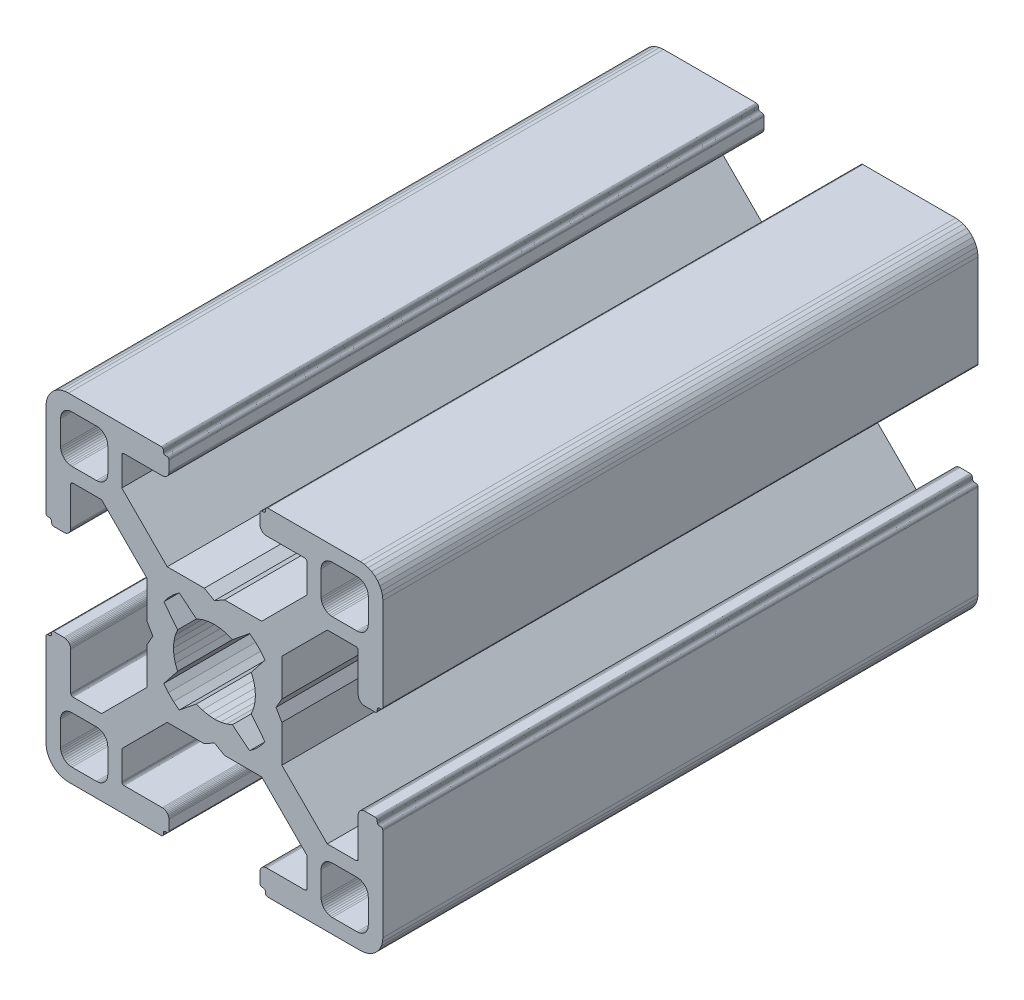
SolidWorks part; units mm, degrees
ref_plane "Front Plane" through (0, 0, 0) normal (0, 0, 1) x (1, 0, 0)
ref_plane "Top Plane" through (0, 0, 0) normal (0, 1, 0) x (1, 0, 0)
ref_plane "Right Plane" through (0, 0, 0) normal (1, 0, 0) x (0, 0, -1)
ref_plane "Plane1" through (0, 0, 0) normal (0, 0, 1) x (1, 0, 0)
sketch "Sketch1" plane through (0, 0, 0) normal (0, 0, 1) x (1, 0, 0)
  line L0 (28.3473, 29.9696) -> (28, 30)
  line L1 (28, 30) -> (19.75, 30)
  line L2 (19.75, 30) -> (19.7153, 29.997)
  line L3 (19.7153, 29.997) -> (19.6816, 29.9879)
  line L4 (19.6816, 29.9879) -> (19.65, 29.9732)
  line L5 (19.65, 29.9732) -> (19.6214, 29.9532)
  line L6 (19.6214, 29.9532) -> (19.5968, 29.9286)
  line L7 (19.5968, 29.9286) -> (19.5768, 29.9)
  line L8 (19.5768, 29.9) -> (19.5621, 29.8684)
  line L9 (19.5621, 29.8684) -> (19.553, 29.8347)
  line L10 (19.553, 29.8347) -> (19.55, 29.8)
  line L11 (19.55, 29.8) -> (19.55, 29.7)
  line L12 (19.55, 29.7) -> (19.547, 29.6653)
  line L13 (19.547, 29.6653) -> (19.5379, 29.6316)
  line L14 (19.5379, 29.6316) -> (19.5232, 29.6)
  line L15 (19.5232, 29.6) -> (19.5032, 29.5714)
  line L16 (19.5032, 29.5714) -> (19.4786, 29.5468)
  line L17 (19.4786, 29.5468) -> (19.45, 29.5268)
  line L18 (19.45, 29.5268) -> (19.4184, 29.5121)
  line L19 (19.4184, 29.5121) -> (19.3847, 29.503)
  line L20 (19.3847, 29.503) -> (19.35, 29.5)
  line L21 (19.35, 29.5) -> (19.25, 29.5)
  line L22 (19.25, 29.5) -> (19.2153, 29.497)
  line L23 (19.2153, 29.497) -> (19.1816, 29.4879)
  line L24 (19.1816, 29.4879) -> (19.15, 29.4732)
  line L25 (19.15, 29.4732) -> (19.1214, 29.4532)
  line L26 (19.1214, 29.4532) -> (19.0968, 29.4286)
  line L27 (19.0968, 29.4286) -> (19.0768, 29.4)
  line L28 (19.0768, 29.4) -> (19.0621, 29.3684)
  line L29 (19.0621, 29.3684) -> (19.053, 29.3347)
  line L30 (19.053, 29.3347) -> (19.05, 29.3)
  line L31 (19.05, 29.3) -> (19.05, 28.4)
  line L32 (19.05, 28.4) -> (19.0591, 28.2958)
  line L33 (19.0591, 28.2958) -> (19.0862, 28.1948)
  line L34 (19.0862, 28.1948) -> (19.1304, 28.1)
  line L35 (19.1304, 28.1) -> (19.1904, 28.0143)
  line L36 (19.1904, 28.0143) -> (19.2643, 27.9404)
  line L37 (19.2643, 27.9404) -> (19.35, 27.8804)
  line L38 (19.35, 27.8804) -> (19.4448, 27.8362)
  line L39 (19.4448, 27.8362) -> (19.5458, 27.8091)
  line L40 (19.5458, 27.8091) -> (19.65, 27.8)
  line L41 (19.65, 27.8) -> (23.05, 27.8)
  line L42 (23.05, 27.8) -> (23.0847, 27.7969)
  line L43 (23.0847, 27.7969) -> (23.1184, 27.7879)
  line L44 (23.1184, 27.7879) -> (23.15, 27.7732)
  line L45 (23.15, 27.7732) -> (23.1786, 27.7532)
  line L46 (23.1786, 27.7532) -> (23.2032, 27.7285)
  line L47 (23.2032, 27.7285) -> (23.2232, 27.7)
  line L48 (23.2232, 27.7) -> (23.2379, 27.6684)
  line L49 (23.2379, 27.6684) -> (23.247, 27.6347)
  line L50 (23.247, 27.6347) -> (23.25, 27.6)
  line L51 (23.25, 27.6) -> (23.25, 25.05)
  line L52 (23.25, 25.05) -> (19.2045, 21)
  line L53 (19.2045, 21) -> (15.9, 21)
  line L54 (15.9, 21) -> (15, 20.4848)
  line L55 (15, 20.4848) -> (14.1, 21)
  line L56 (14.1, 21) -> (10.7955, 21)
  line L57 (10.7955, 21) -> (7.9973, 23.8013)
  line L58 (7.9973, 23.8013) -> (6.75, 25.05)
  line L59 (6.75, 25.05) -> (6.75, 27.6)
  line L60 (6.75, 27.6) -> (6.753, 27.6347)
  line L61 (6.753, 27.6347) -> (6.7621, 27.6684)
  line L62 (6.7621, 27.6684) -> (6.7768, 27.7)
  line L63 (6.7768, 27.7) -> (6.7968, 27.7285)
  line L64 (6.7968, 27.7285) -> (6.8215, 27.7532)
  line L65 (6.8215, 27.7532) -> (6.85, 27.7732)
  line L66 (6.85, 27.7732) -> (6.8816, 27.7879)
  line L67 (6.8816, 27.7879) -> (6.9153, 27.7969)
  line L68 (6.9153, 27.7969) -> (6.95, 27.8)
  line L69 (6.95, 27.8) -> (10.35, 27.8)
  line L70 (10.35, 27.8) -> (10.4542, 27.8091)
  line L71 (10.4542, 27.8091) -> (10.5552, 27.8362)
  line L72 (10.5552, 27.8362) -> (10.65, 27.8804)
  line L73 (10.65, 27.8804) -> (10.7357, 27.9404)
  line L74 (10.7357, 27.9404) -> (10.8096, 28.0143)
  line L75 (10.8096, 28.0143) -> (10.8696, 28.1)
  line L76 (10.8696, 28.1) -> (10.9138, 28.1948)
  line L77 (10.9138, 28.1948) -> (10.9409, 28.2958)
  line L78 (10.9409, 28.2958) -> (10.95, 28.4)
  line L79 (10.95, 28.4) -> (10.95, 29.3)
  line L80 (10.95, 29.3) -> (10.947, 29.3347)
  line L81 (10.947, 29.3347) -> (10.938, 29.3684)
  line L82 (10.938, 29.3684) -> (10.9232, 29.4)
  line L83 (10.9232, 29.4) -> (10.9032, 29.4286)
  line L84 (10.9032, 29.4286) -> (10.8786, 29.4532)
  line L85 (10.8786, 29.4532) -> (10.85, 29.4732)
  line L86 (10.85, 29.4732) -> (10.8184, 29.4879)
  line L87 (10.8184, 29.4879) -> (10.7847, 29.497)
  line L88 (10.7847, 29.497) -> (10.75, 29.5)
  line L89 (10.75, 29.5) -> (10.65, 29.5)
  line L90 (10.65, 29.5) -> (10.6153, 29.503)
  line L91 (10.6153, 29.503) -> (10.5816, 29.5121)
  line L92 (10.5816, 29.5121) -> (10.55, 29.5268)
  line L93 (10.55, 29.5268) -> (10.5214, 29.5468)
  line L94 (10.5214, 29.5468) -> (10.4968, 29.5714)
  line L95 (10.4968, 29.5714) -> (10.4768, 29.6)
  line L96 (10.4768, 29.6) -> (10.4621, 29.6316)
  line L97 (10.4621, 29.6316) -> (10.453, 29.6653)
  line L98 (10.453, 29.6653) -> (10.45, 29.7)
  line L99 (10.45, 29.7) -> (10.45, 29.8)
  line L100 (10.45, 29.8) -> (10.447, 29.8347)
  line L101 (10.447, 29.8347) -> (10.4379, 29.8684)
  line L102 (10.4379, 29.8684) -> (10.4232, 29.9)
  line L103 (10.4232, 29.9) -> (10.4032, 29.9286)
  line L104 (10.4032, 29.9286) -> (10.3786, 29.9532)
  line L105 (10.3786, 29.9532) -> (10.35, 29.9732)
  line L106 (10.35, 29.9732) -> (10.3184, 29.9879)
  line L107 (10.3184, 29.9879) -> (10.2847, 29.997)
  line L108 (10.2847, 29.997) -> (10.25, 30)
  line L109 (10.25, 30) -> (2, 30)
  line L110 (2, 30) -> (1.6527, 29.9696)
  line L111 (1.6527, 29.9696) -> (1.316, 29.8794)
  line L112 (1.316, 29.8794) -> (1, 29.7321)
  line L113 (1, 29.7321) -> (0.7144, 29.5321)
  line L114 (0.7144, 29.5321) -> (0.4679, 29.2856)
  line L115 (0.4679, 29.2856) -> (0.2679, 29)
  line L116 (0.2679, 29) -> (0.1206, 28.684)
  line L117 (0.1206, 28.684) -> (0.0304, 28.3473)
  line L118 (0.0304, 28.3473) -> (0, 28)
  line L119 (0, 28) -> (0, 19.75)
  line L120 (0, 19.75) -> (0.003, 19.7153)
  line L121 (0.003, 19.7153) -> (0.0121, 19.6816)
  line L122 (0.0121, 19.6816) -> (0.0268, 19.65)
  line L123 (0.0268, 19.65) -> (0.0468, 19.6214)
  line L124 (0.0468, 19.6214) -> (0.0714, 19.5968)
  line L125 (0.0714, 19.5968) -> (0.1, 19.5768)
  line L126 (0.1, 19.5768) -> (0.1316, 19.5621)
  line L127 (0.1316, 19.5621) -> (0.1653, 19.553)
  line L128 (0.1653, 19.553) -> (0.2, 19.55)
  line L129 (0.2, 19.55) -> (0.3, 19.55)
  line L130 (0.3, 19.55) -> (0.3347, 19.547)
  line L131 (0.3347, 19.547) -> (0.3684, 19.5379)
  line L132 (0.3684, 19.5379) -> (0.4, 19.5232)
  line L133 (0.4, 19.5232) -> (0.4286, 19.5032)
  line L134 (0.4286, 19.5032) -> (0.4532, 19.4786)
  line L135 (0.4532, 19.4786) -> (0.4732, 19.45)
  line L136 (0.4732, 19.45) -> (0.4879, 19.4184)
  line L137 (0.4879, 19.4184) -> (0.497, 19.3847)
  line L138 (0.497, 19.3847) -> (0.5, 19.35)
  line L139 (0.5, 19.35) -> (0.5, 19.25)
  line L140 (0.5, 19.25) -> (0.503, 19.2153)
  line L141 (0.503, 19.2153) -> (0.5121, 19.1816)
  line L142 (0.5121, 19.1816) -> (0.5268, 19.15)
  line L143 (0.5268, 19.15) -> (0.5468, 19.1214)
  line L144 (0.5468, 19.1214) -> (0.5714, 19.0968)
  line L145 (0.5714, 19.0968) -> (0.6, 19.0768)
  line L146 (0.6, 19.0768) -> (0.6316, 19.0621)
  line L147 (0.6316, 19.0621) -> (0.6653, 19.053)
  line L148 (0.6653, 19.053) -> (0.7, 19.05)
  line L149 (0.7, 19.05) -> (1.6, 19.05)
  line L150 (1.6, 19.05) -> (1.7042, 19.0591)
  line L151 (1.7042, 19.0591) -> (1.8052, 19.0862)
  line L152 (1.8052, 19.0862) -> (1.9, 19.1304)
  line L153 (1.9, 19.1304) -> (1.9857, 19.1904)
  line L154 (1.9857, 19.1904) -> (2.0596, 19.2643)
  line L155 (2.0596, 19.2643) -> (2.1196, 19.35)
  line L156 (2.1196, 19.35) -> (2.1638, 19.4448)
  line L157 (2.1638, 19.4448) -> (2.1909, 19.5458)
  line L158 (2.1909, 19.5458) -> (2.2, 19.65)
  line L159 (2.2, 19.65) -> (2.2, 23.05)
  line L160 (2.2, 23.05) -> (2.203, 23.0847)
  line L161 (2.203, 23.0847) -> (2.2121, 23.1184)
  line L162 (2.2121, 23.1184) -> (2.2268, 23.15)
  line L163 (2.2268, 23.15) -> (2.2468, 23.1786)
  line L164 (2.2468, 23.1786) -> (2.2714, 23.2032)
  line L165 (2.2714, 23.2032) -> (2.3, 23.2232)
  line L166 (2.3, 23.2232) -> (2.3316, 23.2379)
  line L167 (2.3316, 23.2379) -> (2.3653, 23.247)
  line L168 (2.3653, 23.247) -> (2.4, 23.25)
  line L169 (2.4, 23.25) -> (4.95, 23.25)
  line L170 (4.95, 23.25) -> (7.9973, 20.2027)
  line L171 (7.9973, 20.2027) -> (8.9955, 19.2045)
  line L172 (8.9955, 19.2045) -> (8.9955, 15.9)
  line L173 (8.9955, 15.9) -> (9.5151, 15)
  line L174 (9.5151, 15) -> (8.9955, 14.1)
  line L175 (8.9955, 14.1) -> (8.9955, 10.7955)
  line L176 (8.9955, 10.7955) -> (4.95, 6.75)
  line L177 (4.95, 6.75) -> (2.4, 6.75)
  line L178 (2.4, 6.75) -> (2.3653, 6.753)
  line L179 (2.3653, 6.753) -> (2.3316, 6.7621)
  line L180 (2.3316, 6.7621) -> (2.3, 6.7768)
  line L181 (2.3, 6.7768) -> (2.2714, 6.7968)
  line L182 (2.2714, 6.7968) -> (2.2468, 6.8214)
  line L183 (2.2468, 6.8214) -> (2.2268, 6.85)
  line L184 (2.2268, 6.85) -> (2.2121, 6.8816)
  line L185 (2.2121, 6.8816) -> (2.203, 6.9153)
  line L186 (2.203, 6.9153) -> (2.2, 6.95)
  line L187 (2.2, 6.95) -> (2.2, 10.35)
  line L188 (2.2, 10.35) -> (2.1909, 10.4542)
  line L189 (2.1909, 10.4542) -> (2.1638, 10.5552)
  line L190 (2.1638, 10.5552) -> (2.1196, 10.65)
  line L191 (2.1196, 10.65) -> (2.0596, 10.7357)
  line L192 (2.0596, 10.7357) -> (1.9857, 10.8096)
  line L193 (1.9857, 10.8096) -> (1.9, 10.8696)
  line L194 (1.9, 10.8696) -> (1.8052, 10.9138)
  line L195 (1.8052, 10.9138) -> (1.7042, 10.9409)
  line L196 (1.7042, 10.9409) -> (1.6, 10.95)
  line L197 (1.6, 10.95) -> (0.7, 10.95)
  line L198 (0.7, 10.95) -> (0.6653, 10.9469)
  line L199 (0.6653, 10.9469) -> (0.6316, 10.9379)
  line L200 (0.6316, 10.9379) -> (0.6, 10.9232)
  line L201 (0.6, 10.9232) -> (0.5715, 10.9032)
  line L202 (0.5715, 10.9032) -> (0.5468, 10.8785)
  line L203 (0.5468, 10.8785) -> (0.5268, 10.85)
  line L204 (0.5268, 10.85) -> (0.5121, 10.8184)
  line L205 (0.5121, 10.8184) -> (0.503, 10.7847)
  line L206 (0.503, 10.7847) -> (0.5, 10.75)
  line L207 (0.5, 10.75) -> (0.5, 10.65)
  line L208 (0.5, 10.65) -> (0.497, 10.6153)
  line L209 (0.497, 10.6153) -> (0.4879, 10.5816)
  line L210 (0.4879, 10.5816) -> (0.4732, 10.55)
  line L211 (0.4732, 10.55) -> (0.4532, 10.5214)
  line L212 (0.4532, 10.5214) -> (0.4286, 10.4968)
  line L213 (0.4286, 10.4968) -> (0.4, 10.4768)
  line L214 (0.4, 10.4768) -> (0.3684, 10.4621)
  line L215 (0.3684, 10.4621) -> (0.3347, 10.453)
  line L216 (0.3347, 10.453) -> (0.3, 10.45)
  line L217 (0.3, 10.45) -> (0.2, 10.45)
  line L218 (0.2, 10.45) -> (0.1653, 10.447)
  line L219 (0.1653, 10.447) -> (0.1316, 10.4379)
  line L220 (0.1316, 10.4379) -> (0.1, 10.4232)
  line L221 (0.1, 10.4232) -> (0.0714, 10.4032)
  line L222 (0.0714, 10.4032) -> (0.0468, 10.3786)
  line L223 (0.0468, 10.3786) -> (0.0268, 10.35)
  line L224 (0.0268, 10.35) -> (0.0121, 10.3184)
  line L225 (0.0121, 10.3184) -> (0.003, 10.2847)
  line L226 (0.003, 10.2847) -> (0, 10.25)
  line L227 (0, 10.25) -> (0, 2)
  line L228 (0, 2) -> (0.0304, 1.6527)
  line L229 (0.0304, 1.6527) -> (0.1206, 1.316)
  line L230 (0.1206, 1.316) -> (0.2679, 1)
  line L231 (0.2679, 1) -> (0.4679, 0.7144)
  line L232 (0.4679, 0.7144) -> (0.7144, 0.4679)
  line L233 (0.7144, 0.4679) -> (1, 0.2679)
  line L234 (1, 0.2679) -> (1.316, 0.1206)
  line L235 (1.316, 0.1206) -> (1.6527, 0.0304)
  line L236 (1.6527, 0.0304) -> (2, 0)
  line L237 (2, 0) -> (10.25, 0)
  line L238 (10.25, 0) -> (10.2847, 0.003)
  line L239 (10.2847, 0.003) -> (10.3184, 0.0121)
  line L240 (10.3184, 0.0121) -> (10.35, 0.0268)
  line L241 (10.35, 0.0268) -> (10.3786, 0.0468)
  line L242 (10.3786, 0.0468) -> (10.4032, 0.0714)
  line L243 (10.4032, 0.0714) -> (10.4232, 0.1)
  line L244 (10.4232, 0.1) -> (10.4379, 0.1316)
  line L245 (10.4379, 0.1316) -> (10.447, 0.1653)
  line L246 (10.447, 0.1653) -> (10.45, 0.2)
  line L247 (10.45, 0.2) -> (10.45, 0.3)
  line L248 (10.45, 0.3) -> (10.453, 0.3347)
  line L249 (10.453, 0.3347) -> (10.4621, 0.3684)
  line L250 (10.4621, 0.3684) -> (10.4768, 0.4)
  line L251 (10.4768, 0.4) -> (10.4968, 0.4286)
  line L252 (10.4968, 0.4286) -> (10.5214, 0.4532)
  line L253 (10.5214, 0.4532) -> (10.55, 0.4732)
  line L254 (10.55, 0.4732) -> (10.5816, 0.4879)
  line L255 (10.5816, 0.4879) -> (10.6153, 0.497)
  line L256 (10.6153, 0.497) -> (10.65, 0.5)
  line L257 (10.65, 0.5) -> (10.75, 0.5)
  line L258 (10.75, 0.5) -> (10.7847, 0.503)
  line L259 (10.7847, 0.503) -> (10.8184, 0.5121)
  line L260 (10.8184, 0.5121) -> (10.85, 0.5268)
  line L261 (10.85, 0.5268) -> (10.8785, 0.5468)
  line L262 (10.8785, 0.5468) -> (10.9032, 0.5715)
  line L263 (10.9032, 0.5715) -> (10.9232, 0.6)
  line L264 (10.9232, 0.6) -> (10.9379, 0.6316)
  line L265 (10.9379, 0.6316) -> (10.9469, 0.6653)
  line L266 (10.9469, 0.6653) -> (10.95, 0.7)
  line L267 (10.95, 0.7) -> (10.95, 1.6)
  line L268 (10.95, 1.6) -> (10.9409, 1.7042)
  line L269 (10.9409, 1.7042) -> (10.9138, 1.8052)
  line L270 (10.9138, 1.8052) -> (10.8696, 1.9)
  line L271 (10.8696, 1.9) -> (10.8096, 1.9857)
  line L272 (10.8096, 1.9857) -> (10.7357, 2.0596)
  line L273 (10.7357, 2.0596) -> (10.65, 2.1196)
  line L274 (10.65, 2.1196) -> (10.5552, 2.1638)
  line L275 (10.5552, 2.1638) -> (10.4542, 2.1909)
  line L276 (10.4542, 2.1909) -> (10.35, 2.2)
  line L277 (10.35, 2.2) -> (6.95, 2.2)
  line L278 (6.95, 2.2) -> (6.9153, 2.203)
  line L279 (6.9153, 2.203) -> (6.8816, 2.212)
  line L280 (6.8816, 2.212) -> (6.85, 2.2268)
  line L281 (6.85, 2.2268) -> (6.8215, 2.2468)
  line L282 (6.8215, 2.2468) -> (6.7968, 2.2714)
  line L283 (6.7968, 2.2714) -> (6.7768, 2.3)
  line L284 (6.7768, 2.3) -> (6.7621, 2.3316)
  line L285 (6.7621, 2.3316) -> (6.753, 2.3653)
  line L286 (6.753, 2.3653) -> (6.75, 2.4)
  line L287 (6.75, 2.4) -> (6.75, 4.95)
  line L288 (6.75, 4.95) -> (9.7875, 7.9908)
  line L289 (9.7875, 7.9908) -> (10.7955, 9)
  line L290 (10.7955, 9) -> (14.1, 9)
  line L291 (14.1, 9) -> (15, 9.5151)
  line L292 (15, 9.5151) -> (15.9, 9)
  line L293 (15.9, 9) -> (19.2045, 9)
  line L294 (19.2045, 9) -> (20.2126, 7.9908)
  line L295 (20.2126, 7.9908) -> (23.25, 4.95)
  line L296 (23.25, 4.95) -> (23.25, 2.4)
  line L297 (23.25, 2.4) -> (23.247, 2.3653)
  line L298 (23.247, 2.3653) -> (23.2379, 2.3316)
  line L299 (23.2379, 2.3316) -> (23.2232, 2.3)
  line L300 (23.2232, 2.3) -> (23.2032, 2.2714)
  line L301 (23.2032, 2.2714) -> (23.1786, 2.2468)
  line L302 (23.1786, 2.2468) -> (23.15, 2.2268)
  line L303 (23.15, 2.2268) -> (23.1184, 2.212)
  line L304 (23.1184, 2.212) -> (23.0847, 2.203)
  line L305 (23.0847, 2.203) -> (23.05, 2.2)
  line L306 (23.05, 2.2) -> (19.65, 2.2)
  line L307 (19.65, 2.2) -> (19.5458, 2.1909)
  line L308 (19.5458, 2.1909) -> (19.4448, 2.1638)
  line L309 (19.4448, 2.1638) -> (19.35, 2.1196)
  line L310 (19.35, 2.1196) -> (19.2643, 2.0596)
  line L311 (19.2643, 2.0596) -> (19.1904, 1.9857)
  line L312 (19.1904, 1.9857) -> (19.1304, 1.9)
  line L313 (19.1304, 1.9) -> (19.0862, 1.8052)
  line L314 (19.0862, 1.8052) -> (19.0591, 1.7042)
  line L315 (19.0591, 1.7042) -> (19.05, 1.6)
  line L316 (19.05, 1.6) -> (19.05, 0.7)
  line L317 (19.05, 0.7) -> (19.053, 0.6653)
  line L318 (19.053, 0.6653) -> (19.0621, 0.6316)
  line L319 (19.0621, 0.6316) -> (19.0768, 0.6)
  line L320 (19.0768, 0.6) -> (19.0968, 0.5714)
  line L321 (19.0968, 0.5714) -> (19.1214, 0.5468)
  line L322 (19.1214, 0.5468) -> (19.15, 0.5268)
  line L323 (19.15, 0.5268) -> (19.1816, 0.5121)
  line L324 (19.1816, 0.5121) -> (19.2153, 0.503)
  line L325 (19.2153, 0.503) -> (19.25, 0.5)
  line L326 (19.25, 0.5) -> (19.35, 0.5)
  line L327 (19.35, 0.5) -> (19.3847, 0.497)
  line L328 (19.3847, 0.497) -> (19.4184, 0.4879)
  line L329 (19.4184, 0.4879) -> (19.45, 0.4732)
  line L330 (19.45, 0.4732) -> (19.4786, 0.4532)
  line L331 (19.4786, 0.4532) -> (19.5032, 0.4286)
  line L332 (19.5032, 0.4286) -> (19.5232, 0.4)
  line L333 (19.5232, 0.4) -> (19.5379, 0.3684)
  line L334 (19.5379, 0.3684) -> (19.547, 0.3347)
  line L335 (19.547, 0.3347) -> (19.55, 0.3)
  line L336 (19.55, 0.3) -> (19.55, 0.2)
  line L337 (19.55, 0.2) -> (19.553, 0.1653)
  line L338 (19.553, 0.1653) -> (19.5621, 0.1316)
  line L339 (19.5621, 0.1316) -> (19.5768, 0.1)
  line L340 (19.5768, 0.1) -> (19.5968, 0.0714)
  line L341 (19.5968, 0.0714) -> (19.6214, 0.0468)
  line L342 (19.6214, 0.0468) -> (19.65, 0.0268)
  line L343 (19.65, 0.0268) -> (19.6816, 0.0121)
  line L344 (19.6816, 0.0121) -> (19.7153, 0.003)
  line L345 (19.7153, 0.003) -> (19.75, 0)
  line L346 (19.75, 0) -> (28, 0)
  line L347 (28, 0) -> (28.3473, 0.0304)
  line L348 (28.3473, 0.0304) -> (28.684, 0.1206)
  line L349 (28.684, 0.1206) -> (29, 0.2679)
  line L350 (29, 0.2679) -> (29.2856, 0.4679)
  line L351 (29.2856, 0.4679) -> (29.5321, 0.7144)
  line L352 (29.5321, 0.7144) -> (29.7321, 1)
  line L353 (29.7321, 1) -> (29.8794, 1.316)
  line L354 (29.8794, 1.316) -> (29.9696, 1.6527)
  line L355 (29.9696, 1.6527) -> (30, 2)
  line L356 (30, 2) -> (30, 10.25)
  line L357 (30, 10.25) -> (29.997, 10.2847)
  line L358 (29.997, 10.2847) -> (29.988, 10.3184)
  line L359 (29.988, 10.3184) -> (29.9732, 10.35)
  line L360 (29.9732, 10.35) -> (29.9532, 10.3785)
  line L361 (29.9532, 10.3785) -> (29.9286, 10.4032)
  line L362 (29.9286, 10.4032) -> (29.9, 10.4232)
  line L363 (29.9, 10.4232) -> (29.8684, 10.4379)
  line L364 (29.8684, 10.4379) -> (29.8347, 10.447)
  line L365 (29.8347, 10.447) -> (29.8, 10.45)
  line L366 (29.8, 10.45) -> (29.7, 10.45)
  line L367 (29.7, 10.45) -> (29.6649, 10.4534)
  line L368 (29.6649, 10.4534) -> (29.6312, 10.4624)
  line L369 (29.6312, 10.4624) -> (29.5996, 10.4772)
  line L370 (29.5996, 10.4772) -> (29.5711, 10.4972)
  line L371 (29.5711, 10.4972) -> (29.5464, 10.5218)
  line L372 (29.5464, 10.5218) -> (29.5264, 10.5504)
  line L373 (29.5264, 10.5504) -> (29.5117, 10.582)
  line L374 (29.5117, 10.582) -> (29.5027, 10.6156)
  line L375 (29.5027, 10.6156) -> (29.4996, 10.6504)
  line L376 (29.4996, 10.6504) -> (29.4996, 10.7504)
  line L377 (29.4996, 10.7504) -> (29.497, 10.7847)
  line L378 (29.497, 10.7847) -> (29.4879, 10.8184)
  line L379 (29.4879, 10.8184) -> (29.4732, 10.85)
  line L380 (29.4732, 10.85) -> (29.4532, 10.8785)
  line L381 (29.4532, 10.8785) -> (29.4286, 10.9032)
  line L382 (29.4286, 10.9032) -> (29.4, 10.9232)
  line L383 (29.4, 10.9232) -> (29.3684, 10.9379)
  line L384 (29.3684, 10.9379) -> (29.3347, 10.9469)
  line L385 (29.3347, 10.9469) -> (29.3, 10.95)
  line L386 (29.3, 10.95) -> (28.4, 10.95)
  line L387 (28.4, 10.95) -> (28.2958, 10.9409)
  line L388 (28.2958, 10.9409) -> (28.1948, 10.9138)
  line L389 (28.1948, 10.9138) -> (28.1, 10.8696)
  line L390 (28.1, 10.8696) -> (28.0143, 10.8096)
  line L391 (28.0143, 10.8096) -> (27.9404, 10.7357)
  line L392 (27.9404, 10.7357) -> (27.8804, 10.65)
  line L393 (27.8804, 10.65) -> (27.8362, 10.5552)
  line L394 (27.8362, 10.5552) -> (27.8091, 10.4542)
  line L395 (27.8091, 10.4542) -> (27.8, 10.35)
  line L396 (27.8, 10.35) -> (27.8, 6.95)
  line L397 (27.8, 6.95) -> (27.797, 6.9153)
  line L398 (27.797, 6.9153) -> (27.7879, 6.8816)
  line L399 (27.7879, 6.8816) -> (27.7732, 6.85)
  line L400 (27.7732, 6.85) -> (27.7532, 6.8214)
  line L401 (27.7532, 6.8214) -> (27.7286, 6.7968)
  line L402 (27.7286, 6.7968) -> (27.7, 6.7768)
  line L403 (27.7, 6.7768) -> (27.6684, 6.7621)
  line L404 (27.6684, 6.7621) -> (27.6347, 6.753)
  line L405 (27.6347, 6.753) -> (27.6, 6.75)
  line L406 (27.6, 6.75) -> (25.05, 6.75)
  line L407 (25.05, 6.75) -> (23.8092, 7.9908)
  line L408 (23.8092, 7.9908) -> (21.0045, 10.7955)
  line L409 (21.0045, 10.7955) -> (21.0045, 14.1)
  line L410 (21.0045, 14.1) -> (20.4849, 15)
  line L411 (20.4849, 15) -> (21.0045, 15.9)
  line L412 (21.0045, 15.9) -> (21.0045, 19.2045)
  line L413 (21.0045, 19.2045) -> (25.05, 23.25)
  line L414 (25.05, 23.25) -> (27.6, 23.25)
  line L415 (27.6, 23.25) -> (27.6347, 23.247)
  line L416 (27.6347, 23.247) -> (27.6684, 23.2379)
  line L417 (27.6684, 23.2379) -> (27.7, 23.2232)
  line L418 (27.7, 23.2232) -> (27.7286, 23.2032)
  line L419 (27.7286, 23.2032) -> (27.7532, 23.1786)
  line L420 (27.7532, 23.1786) -> (27.7732, 23.15)
  line L421 (27.7732, 23.15) -> (27.7879, 23.1184)
  line L422 (27.7879, 23.1184) -> (27.797, 23.0847)
  line L423 (27.797, 23.0847) -> (27.8, 23.05)
  line L424 (27.8, 23.05) -> (27.8, 19.65)
  line L425 (27.8, 19.65) -> (27.8091, 19.5458)
  line L426 (27.8091, 19.5458) -> (27.8362, 19.4448)
  line L427 (27.8362, 19.4448) -> (27.8804, 19.35)
  line L428 (27.8804, 19.35) -> (27.9404, 19.2643)
  line L429 (27.9404, 19.2643) -> (28.0143, 19.1904)
  line L430 (28.0143, 19.1904) -> (28.1, 19.1304)
  line L431 (28.1, 19.1304) -> (28.1948, 19.0862)
  line L432 (28.1948, 19.0862) -> (28.2958, 19.0591)
  line L433 (28.2958, 19.0591) -> (28.4, 19.05)
  line L434 (28.4, 19.05) -> (29.3, 19.05)
  line L435 (29.3, 19.05) -> (29.3347, 19.053)
  line L436 (29.3347, 19.053) -> (29.3684, 19.0621)
  line L437 (29.3684, 19.0621) -> (29.4, 19.0768)
  line L438 (29.4, 19.0768) -> (29.4282, 19.0971)
  line L439 (29.4282, 19.0971) -> (29.4528, 19.1218)
  line L440 (29.4528, 19.1218) -> (29.4728, 19.1504)
  line L441 (29.4728, 19.1504) -> (29.4876, 19.182)
  line L442 (29.4876, 19.182) -> (29.4966, 19.2156)
  line L443 (29.4966, 19.2156) -> (29.4996, 19.2504)
  line L444 (29.4996, 19.2504) -> (29.4996, 19.3504)
  line L445 (29.4996, 19.3504) -> (29.5027, 19.3851)
  line L446 (29.5027, 19.3851) -> (29.5117, 19.4188)
  line L447 (29.5117, 19.4188) -> (29.5264, 19.4504)
  line L448 (29.5264, 19.4504) -> (29.5464, 19.4789)
  line L449 (29.5464, 19.4789) -> (29.5711, 19.5036)
  line L450 (29.5711, 19.5036) -> (29.5996, 19.5236)
  line L451 (29.5996, 19.5236) -> (29.6312, 19.5383)
  line L452 (29.6312, 19.5383) -> (29.6649, 19.5473)
  line L453 (29.6649, 19.5473) -> (29.7, 19.55)
  line L454 (29.7, 19.55) -> (29.8, 19.55)
  line L455 (29.8, 19.55) -> (29.8347, 19.553)
  line L456 (29.8347, 19.553) -> (29.8684, 19.5621)
  line L457 (29.8684, 19.5621) -> (29.9, 19.5768)
  line L458 (29.9, 19.5768) -> (29.9286, 19.5968)
  line L459 (29.9286, 19.5968) -> (29.9532, 19.6214)
  line L460 (29.9532, 19.6214) -> (29.9732, 19.65)
  line L461 (29.9732, 19.65) -> (29.9879, 19.6816)
  line L462 (29.9879, 19.6816) -> (29.997, 19.7153)
  line L463 (29.997, 19.7153) -> (30, 19.75)
  line L464 (30, 19.75) -> (30, 28)
  line L465 (30, 28) -> (29.9696, 28.3473)
  line L466 (29.9696, 28.3473) -> (29.8794, 28.684)
  line L467 (29.8794, 28.684) -> (29.7321, 29)
  line L468 (29.7321, 29) -> (29.5321, 29.2856)
  line L469 (29.5321, 29.2856) -> (29.2856, 29.5321)
  line L470 (29.2856, 29.5321) -> (29, 29.7321)
  line L471 (29, 29.7321) -> (28.684, 29.8794)
  line L472 (28.684, 29.8794) -> (28.3473, 29.9696)
  line L473 (1.3, 25.5) -> (1.3, 27.7)
  line L474 (1.3, 27.7) -> (1.3123, 27.8564)
  line L475 (1.3123, 27.8564) -> (1.3489, 28.009)
  line L476 (1.3489, 28.009) -> (1.409, 28.154)
  line L477 (1.409, 28.154) -> (1.491, 28.2878)
  line L478 (1.491, 28.2878) -> (1.5929, 28.4071)
  line L479 (1.5929, 28.4071) -> (1.7122, 28.509)
  line L480 (1.7122, 28.509) -> (1.846, 28.591)
  line L481 (1.846, 28.591) -> (1.991, 28.6511)
  line L482 (1.991, 28.6511) -> (2.1436, 28.6877)
  line L483 (2.1436, 28.6877) -> (2.3, 28.7)
  line L484 (2.3, 28.7) -> (4.5, 28.7)
  line L485 (4.5, 28.7) -> (4.6564, 28.6877)
  line L486 (4.6564, 28.6877) -> (4.809, 28.6511)
  line L487 (4.809, 28.6511) -> (4.954, 28.591)
  line L488 (4.954, 28.591) -> (5.0878, 28.509)
  line L489 (5.0878, 28.509) -> (5.2071, 28.4071)
  line L490 (5.2071, 28.4071) -> (5.309, 28.2878)
  line L491 (5.309, 28.2878) -> (5.391, 28.154)
  line L492 (5.391, 28.154) -> (5.4511, 28.009)
  line L493 (5.4511, 28.009) -> (5.4877, 27.8564)
  line L494 (5.4877, 27.8564) -> (5.5, 27.7)
  line L495 (5.5, 27.7) -> (5.5, 25.5)
  line L496 (5.5, 25.5) -> (5.4877, 25.3436)
  line L497 (5.4877, 25.3436) -> (5.4511, 25.191)
  line L498 (5.4511, 25.191) -> (5.391, 25.046)
  line L499 (5.391, 25.046) -> (5.309, 24.9122)
  line L500 (5.309, 24.9122) -> (5.2071, 24.7929)
  line L501 (5.2071, 24.7929) -> (5.0878, 24.691)
  line L502 (5.0878, 24.691) -> (4.954, 24.609)
  line L503 (4.954, 24.609) -> (4.809, 24.5489)
  line L504 (4.809, 24.5489) -> (4.6564, 24.5123)
  line L505 (4.6564, 24.5123) -> (4.5, 24.5)
  line L506 (4.5, 24.5) -> (2.3, 24.5)
  line L507 (2.3, 24.5) -> (2.1436, 24.5123)
  line L508 (2.1436, 24.5123) -> (1.991, 24.5489)
  line L509 (1.991, 24.5489) -> (1.846, 24.609)
  line L510 (1.846, 24.609) -> (1.7122, 24.691)
  line L511 (1.7122, 24.691) -> (1.5929, 24.7929)
  line L512 (1.5929, 24.7929) -> (1.491, 24.9122)
  line L513 (1.491, 24.9122) -> (1.409, 25.046)
  line L514 (1.409, 25.046) -> (1.3489, 25.191)
  line L515 (1.3489, 25.191) -> (1.3123, 25.3436)
  line L516 (1.3123, 25.3436) -> (1.3, 25.5)
  line L517 (25.3436, 28.6877) -> (25.5, 28.7)
  line L518 (25.5, 28.7) -> (27.7, 28.7)
  line L519 (27.7, 28.7) -> (27.8564, 28.6877)
  line L520 (27.8564, 28.6877) -> (28.009, 28.6511)
  line L521 (28.009, 28.6511) -> (28.154, 28.591)
  line L522 (28.154, 28.591) -> (28.2878, 28.509)
  line L523 (28.2878, 28.509) -> (28.4071, 28.4071)
  line L524 (28.4071, 28.4071) -> (28.509, 28.2878)
  line L525 (28.509, 28.2878) -> (28.591, 28.154)
  line L526 (28.591, 28.154) -> (28.6511, 28.009)
  line L527 (28.6511, 28.009) -> (28.6877, 27.8564)
  line L528 (28.6877, 27.8564) -> (28.7, 27.7)
  line L529 (28.7, 27.7) -> (28.7, 25.5)
  line L530 (28.7, 25.5) -> (28.6877, 25.3436)
  line L531 (28.6877, 25.3436) -> (28.6511, 25.191)
  line L532 (28.6511, 25.191) -> (28.591, 25.046)
  line L533 (28.591, 25.046) -> (28.509, 24.9122)
  line L534 (28.509, 24.9122) -> (28.4071, 24.7929)
  line L535 (28.4071, 24.7929) -> (28.2878, 24.691)
  line L536 (28.2878, 24.691) -> (28.154, 24.609)
  line L537 (28.154, 24.609) -> (28.009, 24.5489)
  line L538 (28.009, 24.5489) -> (27.8564, 24.5123)
  line L539 (27.8564, 24.5123) -> (27.7, 24.5)
  line L540 (27.7, 24.5) -> (25.5, 24.5)
  line L541 (25.5, 24.5) -> (25.3436, 24.5123)
  line L542 (25.3436, 24.5123) -> (25.191, 24.5489)
  line L543 (25.191, 24.5489) -> (25.046, 24.609)
  line L544 (25.046, 24.609) -> (24.9122, 24.691)
  line L545 (24.9122, 24.691) -> (24.7929, 24.7929)
  line L546 (24.7929, 24.7929) -> (24.691, 24.9122)
  line L547 (24.691, 24.9122) -> (24.609, 25.046)
  line L548 (24.609, 25.046) -> (24.5489, 25.191)
  line L549 (24.5489, 25.191) -> (24.5123, 25.3436)
  line L550 (24.5123, 25.3436) -> (24.5, 25.5)
  line L551 (24.5, 25.5) -> (24.5, 27.7)
  line L552 (24.5, 27.7) -> (24.5123, 27.8564)
  line L553 (24.5123, 27.8564) -> (24.5489, 28.009)
  line L554 (24.5489, 28.009) -> (24.609, 28.154)
  line L555 (24.609, 28.154) -> (24.691, 28.2878)
  line L556 (24.691, 28.2878) -> (24.7929, 28.4071)
  line L557 (24.7929, 28.4071) -> (24.9122, 28.509)
  line L558 (24.9122, 28.509) -> (25.046, 28.591)
  line L559 (25.046, 28.591) -> (25.191, 28.6511)
  line L560 (25.191, 28.6511) -> (25.3436, 28.6877)
  line L561 (15, 18.65) -> (15.55, 18.6083)
  line L562 (15.55, 18.6083) -> (16.0875, 18.4842)
  line L563 (16.0875, 18.4842) -> (16.6001, 18.2806)
  line L564 (16.6001, 18.2806) -> (18.1359, 19.5184)
  line L565 (18.1359, 19.5184) -> (18.645, 19.1187)
  line L566 (18.645, 19.1187) -> (19.1036, 18.6621)
  line L567 (19.1036, 18.6621) -> (19.5053, 18.1547)
  line L568 (19.5053, 18.1547) -> (18.2806, 16.6001)
  line L569 (18.2806, 16.6001) -> (18.4842, 16.0875)
  line L570 (18.4842, 16.0875) -> (18.6083, 15.55)
  line L571 (18.6083, 15.55) -> (18.65, 15)
  line L572 (18.65, 15) -> (18.6083, 14.45)
  line L573 (18.6083, 14.45) -> (18.4842, 13.9125)
  line L574 (18.4842, 13.9125) -> (18.2806, 13.3999)
  line L575 (18.2806, 13.3999) -> (19.5053, 11.8453)
  line L576 (19.5053, 11.8453) -> (19.1036, 11.3379)
  line L577 (19.1036, 11.3379) -> (18.645, 10.8813)
  line L578 (18.645, 10.8813) -> (18.1359, 10.4816)
  line L579 (18.1359, 10.4816) -> (16.6001, 11.7194)
  line L580 (16.6001, 11.7194) -> (16.0875, 11.5158)
  line L581 (16.0875, 11.5158) -> (15.55, 11.3917)
  line L582 (15.55, 11.3917) -> (15, 11.35)
  line L583 (15, 11.35) -> (14.45, 11.3917)
  line L584 (14.45, 11.3917) -> (13.9125, 11.5158)
  line L585 (13.9125, 11.5158) -> (13.3999, 11.7194)
  line L586 (13.3999, 11.7194) -> (11.8641, 10.4816)
  line L587 (11.8641, 10.4816) -> (11.355, 10.8813)
  line L588 (11.355, 10.8813) -> (10.8964, 11.3379)
  line L589 (10.8964, 11.3379) -> (10.4947, 11.8453)
  line L590 (10.4947, 11.8453) -> (11.7194, 13.3999)
  line L591 (11.7194, 13.3999) -> (11.5158, 13.9125)
  line L592 (11.5158, 13.9125) -> (11.3917, 14.45)
  line L593 (11.3917, 14.45) -> (11.35, 15)
  line L594 (11.35, 15) -> (11.3917, 15.55)
  line L595 (11.3917, 15.55) -> (11.5158, 16.0875)
  line L596 (11.5158, 16.0875) -> (11.7194, 16.6001)
  line L597 (11.7194, 16.6001) -> (10.4947, 18.1547)
  line L598 (10.4947, 18.1547) -> (10.8964, 18.6621)
  line L599 (10.8964, 18.6621) -> (11.355, 19.1187)
  line L600 (11.355, 19.1187) -> (11.8641, 19.5184)
  line L601 (11.8641, 19.5184) -> (13.3999, 18.2806)
  line L602 (13.3999, 18.2806) -> (13.9125, 18.4842)
  line L603 (13.9125, 18.4842) -> (14.45, 18.6083)
  line L604 (14.45, 18.6083) -> (15, 18.65)
  line L605 (4.5, 1.3) -> (2.3, 1.3)
  line L606 (2.3, 1.3) -> (2.1436, 1.3123)
  line L607 (2.1436, 1.3123) -> (1.991, 1.3489)
  line L608 (1.991, 1.3489) -> (1.846, 1.409)
  line L609 (1.846, 1.409) -> (1.7122, 1.491)
  line L610 (1.7122, 1.491) -> (1.5929, 1.5929)
  line L611 (1.5929, 1.5929) -> (1.491, 1.7122)
  line L612 (1.491, 1.7122) -> (1.409, 1.846)
  line L613 (1.409, 1.846) -> (1.3489, 1.991)
  line L614 (1.3489, 1.991) -> (1.3123, 2.1436)
  line L615 (1.3123, 2.1436) -> (1.3, 2.3)
  line L616 (1.3, 2.3) -> (1.3, 4.5)
  line L617 (1.3, 4.5) -> (1.3123, 4.6564)
  line L618 (1.3123, 4.6564) -> (1.3489, 4.809)
  line L619 (1.3489, 4.809) -> (1.409, 4.954)
  line L620 (1.409, 4.954) -> (1.491, 5.0878)
  line L621 (1.491, 5.0878) -> (1.5929, 5.2071)
  line L622 (1.5929, 5.2071) -> (1.7122, 5.309)
  line L623 (1.7122, 5.309) -> (1.846, 5.391)
  line L624 (1.846, 5.391) -> (1.991, 5.4511)
  line L625 (1.991, 5.4511) -> (2.1436, 5.4877)
  line L626 (2.1436, 5.4877) -> (2.3, 5.5)
  line L627 (2.3, 5.5) -> (4.5, 5.5)
  line L628 (4.5, 5.5) -> (4.6564, 5.4877)
  line L629 (4.6564, 5.4877) -> (4.809, 5.4511)
  line L630 (4.809, 5.4511) -> (4.954, 5.391)
  line L631 (4.954, 5.391) -> (5.0878, 5.309)
  line L632 (5.0878, 5.309) -> (5.2071, 5.2071)
  line L633 (5.2071, 5.2071) -> (5.309, 5.0878)
  line L634 (5.309, 5.0878) -> (5.391, 4.954)
  line L635 (5.391, 4.954) -> (5.4511, 4.809)
  line L636 (5.4511, 4.809) -> (5.4877, 4.6564)
  line L637 (5.4877, 4.6564) -> (5.5, 4.5)
  line L638 (5.5, 4.5) -> (5.5, 2.3)
  line L639 (5.5, 2.3) -> (5.4877, 2.1436)
  line L640 (5.4877, 2.1436) -> (5.4511, 1.991)
  line L641 (5.4511, 1.991) -> (5.391, 1.846)
  line L642 (5.391, 1.846) -> (5.309, 1.7122)
  line L643 (5.309, 1.7122) -> (5.2071, 1.5929)
  line L644 (5.2071, 1.5929) -> (5.0878, 1.491)
  line L645 (5.0878, 1.491) -> (4.954, 1.409)
  line L646 (4.954, 1.409) -> (4.809, 1.3489)
  line L647 (4.809, 1.3489) -> (4.6564, 1.3123)
  line L648 (4.6564, 1.3123) -> (4.5, 1.3)
  line L649 (27.7, 1.3) -> (25.5, 1.3)
  line L650 (25.5, 1.3) -> (25.3436, 1.3123)
  line L651 (25.3436, 1.3123) -> (25.191, 1.3489)
  line L652 (25.191, 1.3489) -> (25.046, 1.409)
  line L653 (25.046, 1.409) -> (24.9122, 1.491)
  line L654 (24.9122, 1.491) -> (24.7929, 1.5929)
  line L655 (24.7929, 1.5929) -> (24.691, 1.7122)
  line L656 (24.691, 1.7122) -> (24.609, 1.846)
  line L657 (24.609, 1.846) -> (24.5489, 1.991)
  line L658 (24.5489, 1.991) -> (24.5123, 2.1436)
  line L659 (24.5123, 2.1436) -> (24.5, 2.3)
  line L660 (24.5, 2.3) -> (24.5, 4.5)
  line L661 (24.5, 4.5) -> (24.5123, 4.6564)
  line L662 (24.5123, 4.6564) -> (24.5489, 4.809)
  line L663 (24.5489, 4.809) -> (24.609, 4.954)
  line L664 (24.609, 4.954) -> (24.691, 5.0878)
  line L665 (24.691, 5.0878) -> (24.7929, 5.2071)
  line L666 (24.7929, 5.2071) -> (24.9122, 5.309)
  line L667 (24.9122, 5.309) -> (25.046, 5.391)
  line L668 (25.046, 5.391) -> (25.191, 5.4511)
  line L669 (25.191, 5.4511) -> (25.3436, 5.4877)
  line L670 (25.3436, 5.4877) -> (25.5, 5.5)
  line L671 (25.5, 5.5) -> (27.7, 5.5)
  line L672 (27.7, 5.5) -> (27.8564, 5.4877)
  line L673 (27.8564, 5.4877) -> (28.009, 5.4511)
  line L674 (28.009, 5.4511) -> (28.154, 5.391)
  line L675 (28.154, 5.391) -> (28.2878, 5.309)
  line L676 (28.2878, 5.309) -> (28.4071, 5.2071)
  line L677 (28.4071, 5.2071) -> (28.509, 5.0878)
  line L678 (28.509, 5.0878) -> (28.591, 4.954)
  line L679 (28.591, 4.954) -> (28.6511, 4.809)
  line L680 (28.6511, 4.809) -> (28.6877, 4.6564)
  line L681 (28.6877, 4.6564) -> (28.7, 4.5)
  line L682 (28.7, 4.5) -> (28.7, 2.3)
  line L683 (28.7, 2.3) -> (28.6877, 2.1436)
  line L684 (28.6877, 2.1436) -> (28.6511, 1.991)
  line L685 (28.6511, 1.991) -> (28.591, 1.846)
  line L686 (28.591, 1.846) -> (28.509, 1.7122)
  line L687 (28.509, 1.7122) -> (28.4071, 1.5929)
  line L688 (28.4071, 1.5929) -> (28.2878, 1.491)
  line L689 (28.2878, 1.491) -> (28.154, 1.409)
  line L690 (28.154, 1.409) -> (28.009, 1.3489)
  line L691 (28.009, 1.3489) -> (27.8564, 1.3123)
  line L692 (27.8564, 1.3123) -> (27.7, 1.3)
extrude "Boss-Extrude1" add sketch "Sketch1" against normal blind 53
